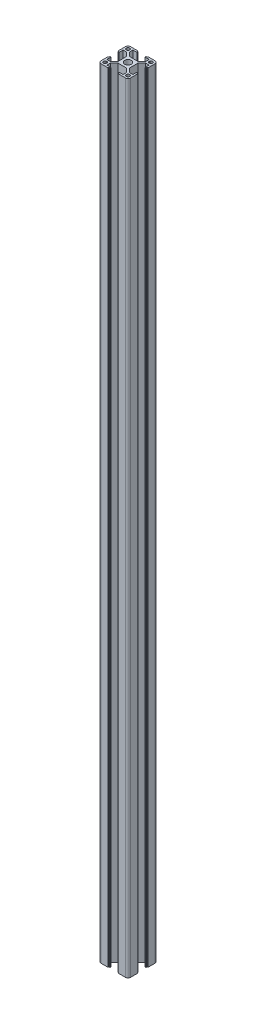
SolidWorks part; units mm, degrees
material "6063-T5"
ref_plane "前视基准面" through (0, 0, 0) normal (0, 0, 1) x (1, 0, 0)
ref_plane "上视基准面" through (0, 0, 0) normal (0, 1, 0) x (1, 0, 0)
ref_plane "右视基准面" through (0, 0, 0) normal (1, 0, 0) x (0, 0, -1)
sketch "草图3" plane through (0, 0, 0) normal (0, 1, 0) x (1, 0, 0)
  line L0 (0, 0) -> (-15, -15) construction
  line L1 (-15, -15) -> (-15, 0) construction
  line L2 (-15, 0) -> (0, 0) construction
  line L3 (-15, -12.5) -> (-15, -5.4)
  line L4 (-14.8, -5.2) -> (-14.4, -5.2)
  line L5 (-14.2, -5) -> (-14.2, -4.3)
  line L6 (-14, -4.1) -> (-13.2, -4.1)
  line L7 (-13.2, -4.1) -> (-13.2, -8.25)
  line L8 (-13.2, -8.25) -> (-9.5228, -8.25)
  line L9 (-9.5228, -8.25) -> (-5.8, -4.5272)
  line L10 (-5.8, -4.5272) -> (-5.8, 4.5272)
  line L11 (-13.2, -12.2) -> (-13.2, -11.05)
  line L12 (-12.2, -10.05) -> (-11.05, -10.05)
  line L13 (-4.5272, -5.8) -> (4.5272, -5.8)
  line L14 (-8.25, -9.5228) -> (-4.5272, -5.8)
  line L15 (-12.2, -13.2) -> (-11.05, -13.2)
  line L16 (-10.05, -12.2) -> (-10.05, -11.05)
  line L17 (-5.2, -14.8) -> (-5.2, -14.4)
  line L18 (-5, -14.2) -> (-4.3, -14.2)
  line L19 (-4.1, -14) -> (-4.1, -13.2)
  line L20 (-4.1, -13.2) -> (-8.25, -13.2)
  line L21 (-8.25, -13.2) -> (-8.25, -9.5228)
  line L22 (-12.5, -15) -> (-5.4, -15)
  line L23 (-12.5, 15) -> (-5.4, 15)
  line L24 (-8.25, 13.2) -> (-8.25, 9.5228)
  line L25 (-4.1, 13.2) -> (-8.25, 13.2)
  line L26 (-4.1, 14) -> (-4.1, 13.2)
  line L27 (-5, 14.2) -> (-4.3, 14.2)
  line L28 (-5.2, 14.8) -> (-5.2, 14.4)
  line L29 (-10.05, 12.2) -> (-10.05, 11.05)
  line L30 (-12.2, 13.2) -> (-11.05, 13.2)
  line L31 (-8.25, 9.5228) -> (-4.5272, 5.8)
  line L32 (-4.5272, 5.8) -> (4.5272, 5.8)
  line L33 (-12.2, 10.05) -> (-11.05, 10.05)
  line L34 (-13.2, 12.2) -> (-13.2, 11.05)
  line L35 (-9.5228, 8.25) -> (-5.8, 4.5272)
  line L36 (-13.2, 8.25) -> (-9.5228, 8.25)
  line L37 (-13.2, 4.1) -> (-13.2, 8.25)
  line L38 (-14, 4.1) -> (-13.2, 4.1)
  line L39 (-14.2, 5) -> (-14.2, 4.3)
  line L40 (-14.8, 5.2) -> (-14.4, 5.2)
  line L41 (-15, 12.5) -> (-15, 5.4)
  line L42 (0, 0) -> (0, -12.3268) construction
  line L43 (15, 12.5) -> (15, 5.4)
  line L44 (14.8, 5.2) -> (14.4, 5.2)
  line L45 (14.2, 5) -> (14.2, 4.3)
  line L46 (14, 4.1) -> (13.2, 4.1)
  line L47 (13.2, 4.1) -> (13.2, 8.25)
  line L48 (13.2, 8.25) -> (9.5228, 8.25)
  line L49 (9.5228, 8.25) -> (5.8, 4.5272)
  line L50 (13.2, 12.2) -> (13.2, 11.05)
  line L51 (12.2, 10.05) -> (11.05, 10.05)
  line L52 (8.25, 9.5228) -> (4.5272, 5.8)
  line L53 (12.2, 13.2) -> (11.05, 13.2)
  line L54 (10.05, 12.2) -> (10.05, 11.05)
  line L55 (5.2, 14.8) -> (5.2, 14.4)
  line L56 (5, 14.2) -> (4.3, 14.2)
  line L57 (4.1, 14) -> (4.1, 13.2)
  line L58 (4.1, 13.2) -> (8.25, 13.2)
  line L59 (8.25, 13.2) -> (8.25, 9.5228)
  line L60 (12.5, 15) -> (5.4, 15)
  line L61 (12.5, -15) -> (5.4, -15)
  line L62 (8.25, -13.2) -> (8.25, -9.5228)
  line L63 (4.1, -13.2) -> (8.25, -13.2)
  line L64 (4.1, -14) -> (4.1, -13.2)
  line L65 (5, -14.2) -> (4.3, -14.2)
  line L66 (5.2, -14.8) -> (5.2, -14.4)
  line L67 (10.05, -12.2) -> (10.05, -11.05)
  line L68 (12.2, -13.2) -> (11.05, -13.2)
  line L69 (8.25, -9.5228) -> (4.5272, -5.8)
  line L70 (12.2, -10.05) -> (11.05, -10.05)
  line L71 (13.2, -12.2) -> (13.2, -11.05)
  line L72 (5.8, -4.5272) -> (5.8, 4.5272)
  line L73 (9.5228, -8.25) -> (5.8, -4.5272)
  line L74 (13.2, -8.25) -> (9.5228, -8.25)
  line L75 (13.2, -4.1) -> (13.2, -8.25)
  line L76 (14, -4.1) -> (13.2, -4.1)
  line L77 (14.2, -5) -> (14.2, -4.3)
  line L78 (14.8, -5.2) -> (14.4, -5.2)
  line L79 (15, -12.5) -> (15, -5.4)
  circle A0 centre (0, 0) radius 3.4
  arc A1 (-12.5, 15) -> (-15, 12.5) centre (-12.5, 12.5) ccw
  arc A2 (15, 12.5) -> (12.5, 15) centre (12.5, 12.5) ccw
  arc A3 (12.5, -15) -> (15, -12.5) centre (12.5, -12.5) ccw
  arc A4 (-15, -12.5) -> (-12.5, -15) centre (-12.5, -12.5) ccw
  arc A5 (-12.2, 13.2) -> (-13.2, 12.2) centre (-12.2, 12.2) ccw
  arc A6 (-12.2, 10.05) -> (-13.2, 11.05) centre (-12.2, 11.05) cw
  arc A7 (-10.05, 11.05) -> (-11.05, 10.05) centre (-11.05, 11.05) cw
  arc A8 (-10.05, 12.2) -> (-11.05, 13.2) centre (-11.05, 12.2) ccw
  arc A9 (11.05, 10.05) -> (10.05, 11.05) centre (11.05, 11.05) cw
  arc A10 (11.05, 13.2) -> (10.05, 12.2) centre (11.05, 12.2) ccw
  arc A11 (13.2, 12.2) -> (12.2, 13.2) centre (12.2, 12.2) ccw
  arc A12 (13.2, 11.05) -> (12.2, 10.05) centre (12.2, 11.05) cw
  arc A13 (12.2, -10.05) -> (13.2, -11.05) centre (12.2, -11.05) cw
  arc A14 (10.05, -11.05) -> (11.05, -10.05) centre (11.05, -11.05) cw
  arc A15 (10.05, -12.2) -> (11.05, -13.2) centre (11.05, -12.2) ccw
  arc A16 (12.2, -13.2) -> (13.2, -12.2) centre (12.2, -12.2) ccw
  arc A17 (-13.2, -11.05) -> (-12.2, -10.05) centre (-12.2, -11.05) cw
  arc A18 (-11.05, -10.05) -> (-10.05, -11.05) centre (-11.05, -11.05) cw
  arc A19 (-11.05, -13.2) -> (-10.05, -12.2) centre (-11.05, -12.2) ccw
  arc A20 (-13.2, -12.2) -> (-12.2, -13.2) centre (-12.2, -12.2) ccw
  arc A21 (-15, -5.4) -> (-14.8, -5.2) centre (-14.8, -5.4) cw
  arc A22 (-14.4, -5.2) -> (-14.2, -5) centre (-14.4, -5) ccw
  arc A23 (-14.2, -4.3) -> (-14, -4.1) centre (-14, -4.3) cw
  arc A24 (-14, 4.1) -> (-14.2, 4.3) centre (-14, 4.3) cw
  arc A25 (-14.2, 5) -> (-14.4, 5.2) centre (-14.4, 5) ccw
  arc A26 (-14.8, 5.2) -> (-15, 5.4) centre (-14.8, 5.4) cw
  arc A27 (-5.4, 15) -> (-5.2, 14.8) centre (-5.4, 14.8) cw
  arc A28 (-5, 14.2) -> (-5.2, 14.4) centre (-5, 14.4) cw
  arc A29 (-4.1, 14) -> (-4.3, 14.2) centre (-4.3, 14) ccw
  arc A30 (5.2, 14.8) -> (5.4, 15) centre (5.4, 14.8) cw
  arc A31 (5.2, 14.4) -> (5, 14.2) centre (5, 14.4) cw
  arc A32 (4.3, 14.2) -> (4.1, 14) centre (4.3, 14) ccw
  arc A33 (15, 5.4) -> (14.8, 5.2) centre (14.8, 5.4) cw
  arc A34 (14.4, 5.2) -> (14.2, 5) centre (14.4, 5) ccw
  arc A35 (14.2, 4.3) -> (14, 4.1) centre (14, 4.3) cw
  arc A36 (14, -4.1) -> (14.2, -4.3) centre (14, -4.3) cw
  arc A37 (14.2, -5) -> (14.4, -5.2) centre (14.4, -5) ccw
  arc A38 (14.8, -5.2) -> (15, -5.4) centre (14.8, -5.4) cw
  arc A39 (5.4, -15) -> (5.2, -14.8) centre (5.4, -14.8) cw
  arc A40 (5, -14.2) -> (5.2, -14.4) centre (5, -14.4) cw
  arc A41 (4.1, -14) -> (4.3, -14.2) centre (4.3, -14) ccw
  arc A42 (-5.2, -14.4) -> (-5, -14.2) centre (-5, -14.4) cw
  arc A43 (-4.3, -14.2) -> (-4.1, -14) centre (-4.3, -14) ccw
  arc A44 (-5.2, -14.8) -> (-5.4, -15) centre (-5.4, -14.8) cw
  point P38 (-5.8, 0)
  point P46 (0, 5.8)
  point P47 (0, -5.8)
  point P83 (5.8, 0)
  point P87 (-15, 15)
  point P90 (15, 15)
  point P93 (15, -15)
  point P99 (-13.2, 13.2)
  point P102 (-13.2, 10.05)
  point P105 (-10.05, 10.05)
  point P108 (-10.05, 13.2)
  point P111 (10.05, 10.05)
  point P114 (10.05, 13.2)
  point P117 (13.2, 13.2)
  point P120 (13.2, 10.05)
  point P123 (13.2, -10.05)
  point P126 (10.05, -10.05)
  point P129 (10.05, -13.2)
  point P132 (13.2, -13.2)
  point P135 (-13.2, -10.05)
  point P138 (-10.05, -10.05)
  point P141 (-10.05, -13.2)
  point P144 (-13.2, -13.2)
  point P147 (-15, -5.2)
  point P150 (-14.2, -5.2)
  point P153 (-14.2, -4.1)
  point P156 (-14.2, 4.1)
  point P159 (-14.2, 5.2)
  point P162 (-15, 5.2)
  point P165 (-5.2, 15)
  point P168 (-5.2, 14.2)
  point P171 (-4.1, 14.2)
  point P174 (5.2, 15)
  point P177 (5.2, 14.2)
  point P180 (4.1, 14.2)
  point P183 (15, 5.2)
  point P186 (14.2, 5.2)
  point P189 (14.2, 4.1)
  point P192 (14.2, -4.1)
  point P195 (14.2, -5.2)
  point P198 (15, -5.2)
  point P201 (5.2, -15)
  point P204 (5.2, -14.2)
  point P207 (4.1, -14.2)
  point P210 (-5.2, -14.2)
  point P213 (-4.1, -14.2)
  point P216 (-5.2, -15)
  dimension "D11" = 6.8
  dimension "D12" = 2.5
  dimension "D13" = 1
  dimension "D14" = 0.2
  dimension "D2" = 15
  dimension "D3" = 4.1
  dimension "D4" = 5.2
  dimension "D5" = 0.8
  dimension "D6" = 1.8
  dimension "D7" = 9.2
  dimension "D8" = 8.25
  dimension "D9" = 0.9
  dimension "D10" = 1.8
extrude "凸台-拉伸1" add sketch "草图3" along normal blind 789
ref_plane "基准面1" through (-10.05, 394.5, 12.2) normal (0, -1, 0) x (-1, 0, 0)
sketch "草图4" plane through (0, 0, 5.8) normal (0, 0, 1) x (1, 0, 0)
  line L1 (-4.5272, 789) -> (4.5272, 789) construction
  line L2 (5.4, 0) -> (12.5, 0) construction
  circle A1 centre (0, 609) radius 3
  circle A2 centre (0, 180) radius 3
  dimension "D2" = 6
  dimension "D3" = 6
  dimension "D4" = 180
  dimension "D5" = 180
extrude "切除-拉伸1" cut sketch "草图4" against normal blind 86
